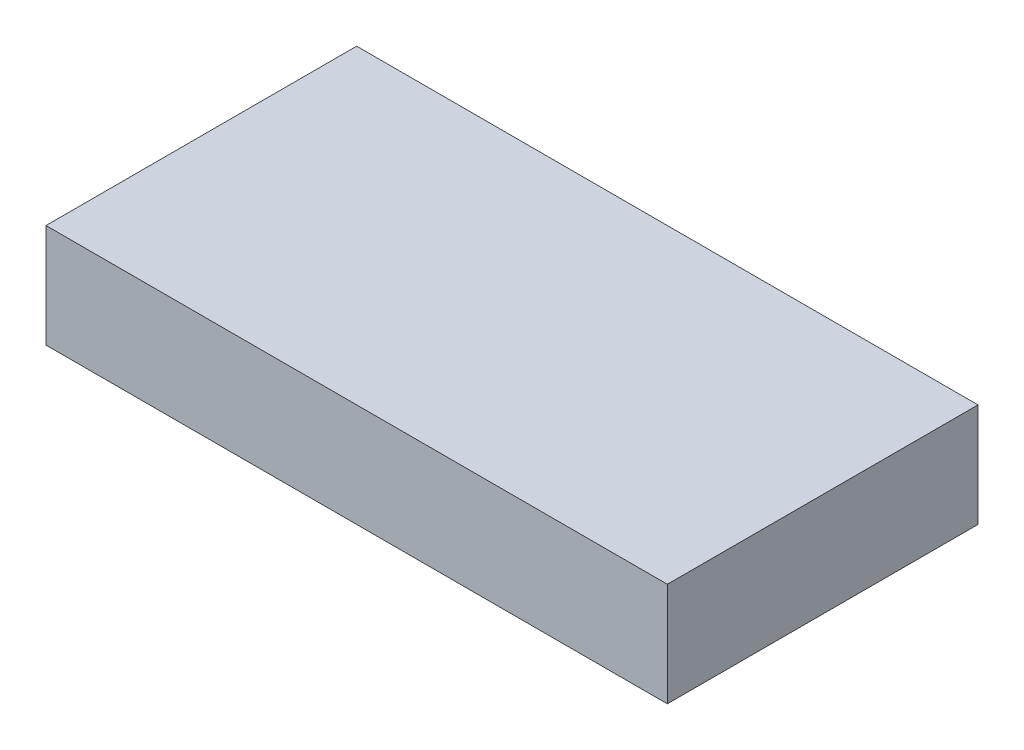
SolidWorks part; units mm, degrees
ref_plane "Front Plane" through (0, 0, 0) normal (0, 0, 1) x (1, 0, 0)
ref_plane "Top Plane" through (0, 0, 0) normal (0, 1, 0) x (1, 0, 0)
ref_plane "Right Plane" through (0, 0, 0) normal (1, 0, 0) x (0, 0, -1)
sketch "Sketch1" plane through (0, 0, 0) normal (0, 1, 0) x (1, 0, 0)
  line L1 (-15, 7.5) -> (15, 7.5)
  line L2 (-15, 7.5) -> (-15, -7.5)
  line L3 (-15, -7.5) -> (15, -7.5)
  line L4 (15, 7.5) -> (15, -7.5)
  line L5 (-15, 7.5) -> (15, -7.5) construction
  line L6 (-15, -7.5) -> (15, 7.5) construction
  point P0 (0, 0)
  dimension "D1" = 30
  dimension "D2" = 15
extrude "Boss-Extrude1" add sketch "Sketch1" along normal blind 5
